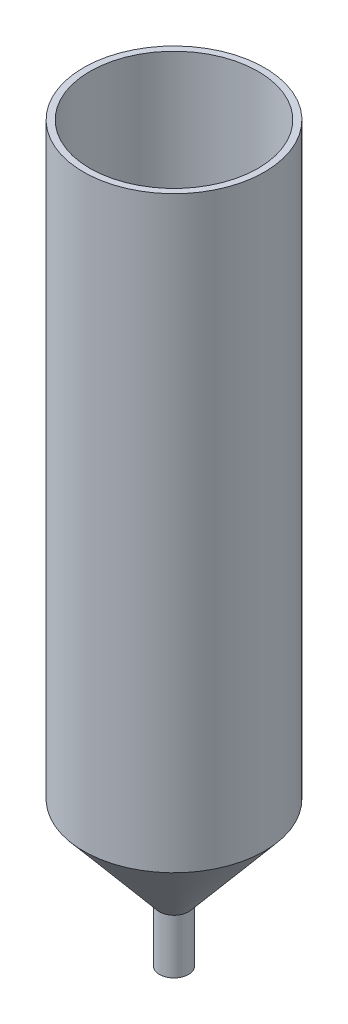
SolidWorks part; units mm, degrees
ref_plane "Front Plane" through (0, 0, 0) normal (0, 0, 1) x (1, 0, 0)
ref_plane "Top Plane" through (0, 0, 0) normal (0, 1, 0) x (1, 0, 0)
ref_plane "Right Plane" through (0, 0, 0) normal (1, 0, 0) x (0, 0, -1)
sketch "Sketch1" plane through (0, 0, 0) normal (0, 0, 1) x (1, 0, 0)
  line L0 (0, 8.0005) -> (0, -33.9283) construction
  line L1 (-18.5816, 0) -> (-18.5816, -129.4837)
  line L2 (-18.5816, -129.4837) -> (-2.218, -148.9851)
  line L4 (-20, 0) -> (-20, -130)
  line L5 (-20, -130) -> (-3.218, -150)
  line L7 (-20, 0) -> (-18.5816, 0)
  line L9 (-3.218, -150) -> (-3.218, -162)
  line L10 (-3.218, -150) -> (21.8625, -170.4213) construction
  line L11 (-2.218, -148.9851) -> (22.7581, -169.3214) construction
  line L12 (-2.218, -148.9851) -> (-2.218, -162)
  line L13 (-2.218, -162) -> (-3.218, -162)
  dimension "D1" = 130
  dimension "D2" = 12
  dimension "D3" = 13.0149
  dimension "D4" = 20
  dimension "D5" = 1
  dimension "D6" = 20
  dimension "D7" = 140
  dimension "D8" = 1.4184
  dimension "D9" = 0
  dimension "D10" = 2.218
revolve "Revolve2" add sketch "Sketch1" angle 360 about L0
